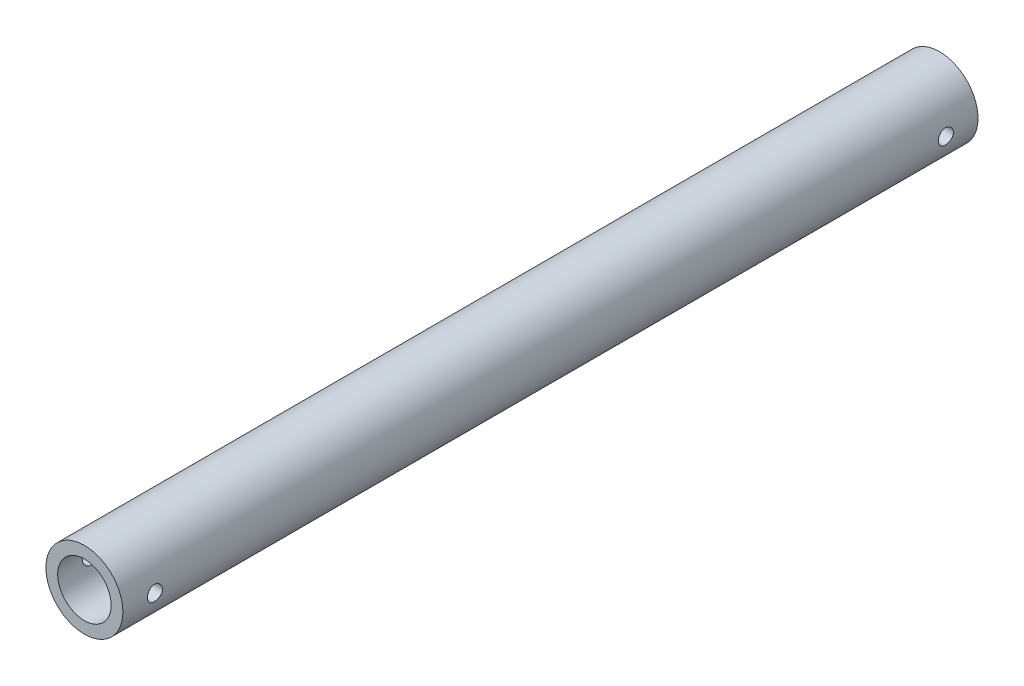
SolidWorks part; units mm, degrees
material "ﾎﾟﾘ塩化ﾋﾞﾆﾙ(PVC)硬質"
ref_plane "正面(Front)" through (0, 0, 0) normal (0, 0, 1) x (1, 0, 0)
ref_plane "平面(Top)" through (0, 0, 0) normal (0, 1, 0) x (1, 0, 0)
ref_plane "右側面(Right)" through (0, 0, 0) normal (1, 0, 0) x (0, 0, -1)
sketch "ｽｹｯﾁ1" plane through (0, 0, 0) normal (0, 0, 1) x (1, 0, 0)
  circle A0 centre (0, 0) radius 9
  circle A1 centre (0, 0) radius 6.25
  dimension "D1" = 18
  dimension "D2" = 12.5
extrude "ﾎﾞｽ - 押し出し1" add sketch "ｽｹｯﾁ1" along normal blind 200
sketch "ｽｹｯﾁ2" plane through (0, 0, 0) normal (1, 0, 0) x (0, 0, -1)
  line L0 (0, 0) -> (-231.2557, 0) construction
  line L1 (0, -9) -> (0, 9) construction
  line L2 (-200, 9) -> (-200, -9) construction
  circle A0 centre (-7.5, 0) radius 1.75
  circle A1 centre (-192.5, 0) radius 1.75
  point P11 (-7.5, 0)
  dimension "D2" = 7.5
  dimension "D3" = 3.5
  dimension "D1" = 7.5
extrude "ｶｯﾄ - 押し出し1" cut sketch "ｽｹｯﾁ2" against normal through all both and the other way through all
